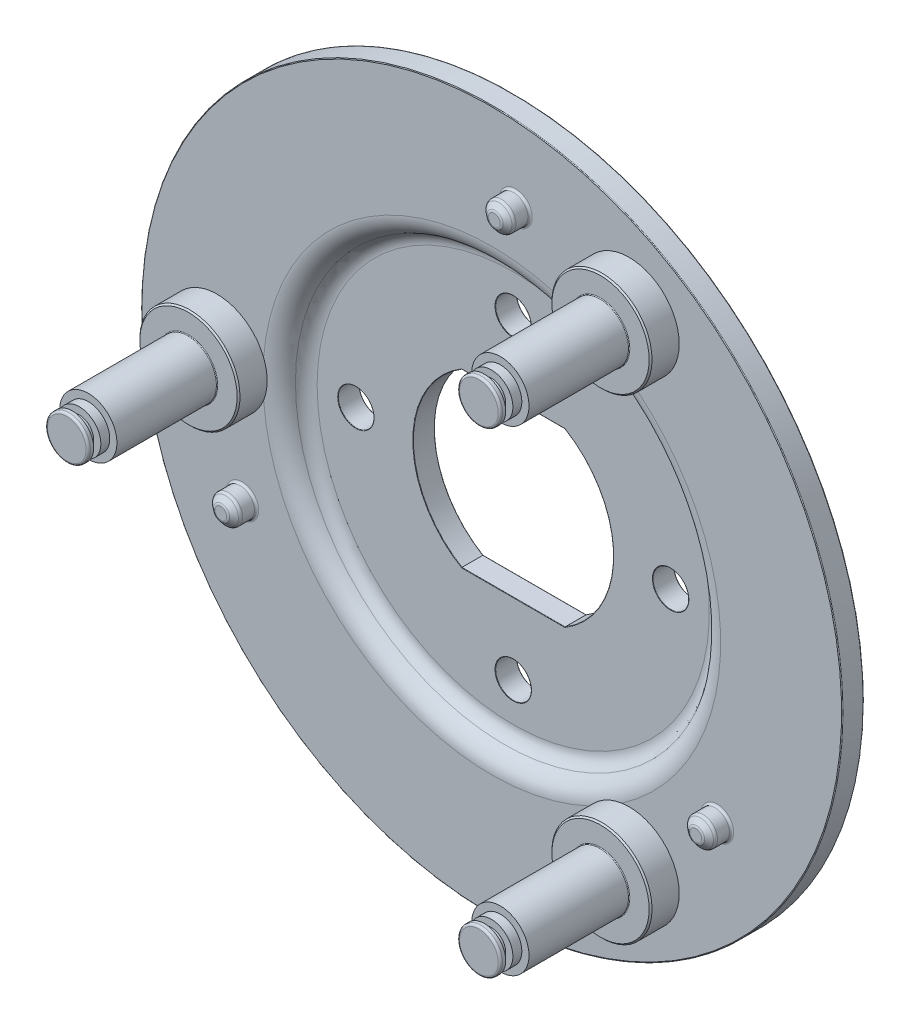
SolidWorks part; units mm, degrees
ref_plane "Piano frontale" through (0, 0, 0) normal (0, 0, 1) x (1, 0, 0)
ref_plane "Piano superiore" through (0, 0, 0) normal (0, 1, 0) x (1, 0, 0)
ref_plane "Piano destro" through (0, 0, 0) normal (1, 0, 0) x (0, 0, -1)
sketch "Schizzo14" plane through (0, 0, 0) normal (0, 1, 0) x (1, 0, 0)
  line L7 (0, 6) -> (29, 6)
  line L9 (49, 3) -> (32, 3)
  line L10 (49, 3) -> (49, 6)
  line L13 (29, 9) -> (0, 9)
  line L14 (0, 9) -> (0, 6)
  line L17 (32, 6) -> (49, 6)
  arc A2 (32, 6) -> (29, 9) centre (29, 6) ccw
  arc A3 (29, 6) -> (32, 3) centre (32, 6) ccw
revolve "Rivoluzione1" add sketch "Schizzo14" angle 360 about L14
fillet "Raccordo1" radius 2 2 edges at (-32, 0, -6) (-29, 0, -6)
fillet "Raccordo2" radius 0.1 2 edges at (-49, 0, -3) (-49, 0, -6)
sketch "Schizzo15" plane through (0, 0, -6) normal (0, 0, 1) x (1, 0, 0)
  line L1 (-7.2111, -12) -> (7.2111, -12)
  line L3 (7.2111, 12) -> (-7.2111, 12)
  arc A0 (-7.2111, 12) -> (-7.2111, -12) centre (0, 0) ccw
  arc A1 (7.2111, -12) -> (7.2111, 12) centre (0, 0) ccw
extrude "Taglio-Estrusione1" cut sketch "Schizzo15" against normal through all
sketch "Schizzo16" plane through (0, 0, -6) normal (0, 0, 1) x (1, 0, 0)
  line L0 (0, 0) -> (-22, 0) construction
  circle A0 centre (-22, 0) radius 2.5
  circle A1 centre (0, 22) radius 2.5
  circle A2 centre (22, 0) radius 2.5
  circle A3 centre (0, -22) radius 2.5
  point P12 (0, 0)
  dimension "D1" = 4
extrude "Taglio-Estrusione2" cut sketch "Schizzo16" against normal through all
sketch "Schizzo18" plane through (0, 0, -3) normal (0, 0, 1) x (1, 0, 0)
  circle A3 centre (3.3537, 38.3325) radius 0.5
  point P9 (0, 0)
extrude "Taglio-Estrusione4" cut sketch "Schizzo18" against normal blind 5
pattern_circular "RipetizioneCircolare1" count 3 over 360 about axis through (0, 0, 0) along (0, 0, 1) of "Taglio-Estrusione4"
sketch "Schizzo19" plane through (0, 0, -6) normal (0, 0, -1) x (-1, 0, 0)
  circle A0 centre (-3.3537, 38.3325) radius 3.5
  circle A1 centre (34.8737, -16.2619) radius 3.5
  circle A2 centre (-31.5201, -22.0706) radius 3.5
  point P8 (0, 0)
  dimension "D1" = 3
extrude "Taglio-Estrusione5" cut sketch "Schizzo19" against normal blind 1.5
sketch "Schizzo20" plane through (0, 0, -6) normal (0, 0, -1) x (-1, 0, 0)
  line L1 (38.4, 0) -> (42.9, 0)
sketch "Schizzo21" plane through (0, 0, 0) normal (0, 1, 0) x (1, 0, 0)
  line L0 (-38.9, 6) -> (-42.4, 6)
  line L1 (-42.9, 6.5) -> (-42.9, 6.75)
  line L2 (-42.4, 7.25) -> (-40.4, 7.25)
  line L6 (-38.9, 6) -> (-38.4, 6)
  line L9 (-38.4, 6) -> (-38.4, 6.0358)
  line L12 (-40.4, 7.25) -> (-38.506, 6.0662)
  arc A1 (-42.9, 6.75) -> (-42.4, 7.25) centre (-42.4, 6.75) cw
  arc A2 (-42.4, 6) -> (-42.9, 6.5) centre (-42.4, 6.5) cw
  arc A4 (-38.4, 6.0358) -> (-38.506, 6.0662) centre (-38.4, 6.2358) cw
  dimension "D1" = 0.2
revolve "Rivoluzione2" add sketch "Schizzo21" angle 360 about L9
pattern_circular "RipetizioneCircolare2" count 3 over 360 about axis through (0, 0, 0) along (0, 0, 1) of "Rivoluzione2"
sketch "Schizzo22" plane through (0, 0, -3) normal (0, 0, 1) x (1, 0, 0)
  circle A0 centre (-38.4, 0) radius 7
extrude "Estrusione-Estrusione2" add sketch "Schizzo22" along normal blind 4
sketch "Schizzo23" plane through (0, 0, 1) normal (0, 0, 1) x (1, 0, 0)
  circle A0 centre (-38.4, 0) radius 4
extrude "Estrusione-Estrusione3" add sketch "Schizzo23" along normal blind 14
sketch "Schizzo24" plane through (0, 0, 0) normal (0, 1, 0) x (1, 0, 0)
  line L0 (-38.4, -15) -> (-35.4, -15)
  line L1 (-35.4, -15) -> (-35.4, -16.25)
  line L2 (-38.4, -15) -> (-38.4, -18)
  line L3 (-35.4, -17.25) -> (-35.4, -18)
  line L4 (-35.4, -16.25) -> (-36.4, -16.25)
  line L5 (-36.4, -16.25) -> (-36.4, -17.25)
  line L6 (-36.4, -17.25) -> (-35.4, -17.25)
  line L7 (-38.4, -18) -> (-35.4, -18)
revolve "Rivoluzione3" add sketch "Schizzo24" angle 360 about L2
pattern_circular "RipetizioneCircolare3" count 3 over 360 about axis through (0, 0, 0) along (0, 0, 1) of "Estrusione-Estrusione2", "Estrusione-Estrusione3", "Rivoluzione3"
chamfer "Smusso1" distance 0.2 angle 45 3 edges at (15.7, -27.1932, 1) (15.7, 27.1932, 1) (-31.4, 0, 1)
fillet "Raccordo3" radius 0.3 3 edges at (-41.4, 0, 18) (20.7, -35.8535, 18) (20.7, 35.8535, 18)
fillet "Raccordo4" radius 0.1 3 edges at (17.2, 29.7913, 1) (17.2, -29.7913, 1) (-34.4, 0, 1)
sketch "Schizzo25" plane through (0, 0, -3) normal (0, 0, 1) x (1, 0, 0)
  circle A0 centre (3.3537, 38.3325) radius 2
extrude "Estrusione-Estrusione4" add sketch "Schizzo25" along normal blind 3
chamfer "Smusso2" distance 0.8 distance2 1 1 edges at (5.3537, 38.3325, 0)
fillet "Raccordo7" radius 0.5 2 edges at (4.3537, 38.3325, 0) (5.3537, 38.3325, -0.8)
pattern_circular "RipetizioneCircolare5" count 3 over 360 about axis through (0, 0, 0) along (0, 0, 1) of "Estrusione-Estrusione4", "Smusso2", "Raccordo7"
fillet "Raccordo8" radius 0.05 18 edges at (0, 12, -9) (-19.5, 0, -6) (-19.5, 0, -9) (2.5, 22, -6) (2.5, 22, -9) (24.5, 0, -6) (24.5, 0, -9) (2.5, -22, -6) (2.5, -22, -9) (0, 12, -6) (7.2111, 12, -7.5) (-14, 0, -9) (-14, 0, -6) (14, 0, -9) (7.2111, -12, -7.5) (0, -12, -9) (0, -12, -6) (14, 0, -6)
fillet "Raccordo9" radius 0.3 3 edges at (-36.8737, -16.2619, -3) (1.3537, 38.3325, -3) (29.5201, -22.0706, -3)
equation "\"0.0.5mm\"=0.1"
